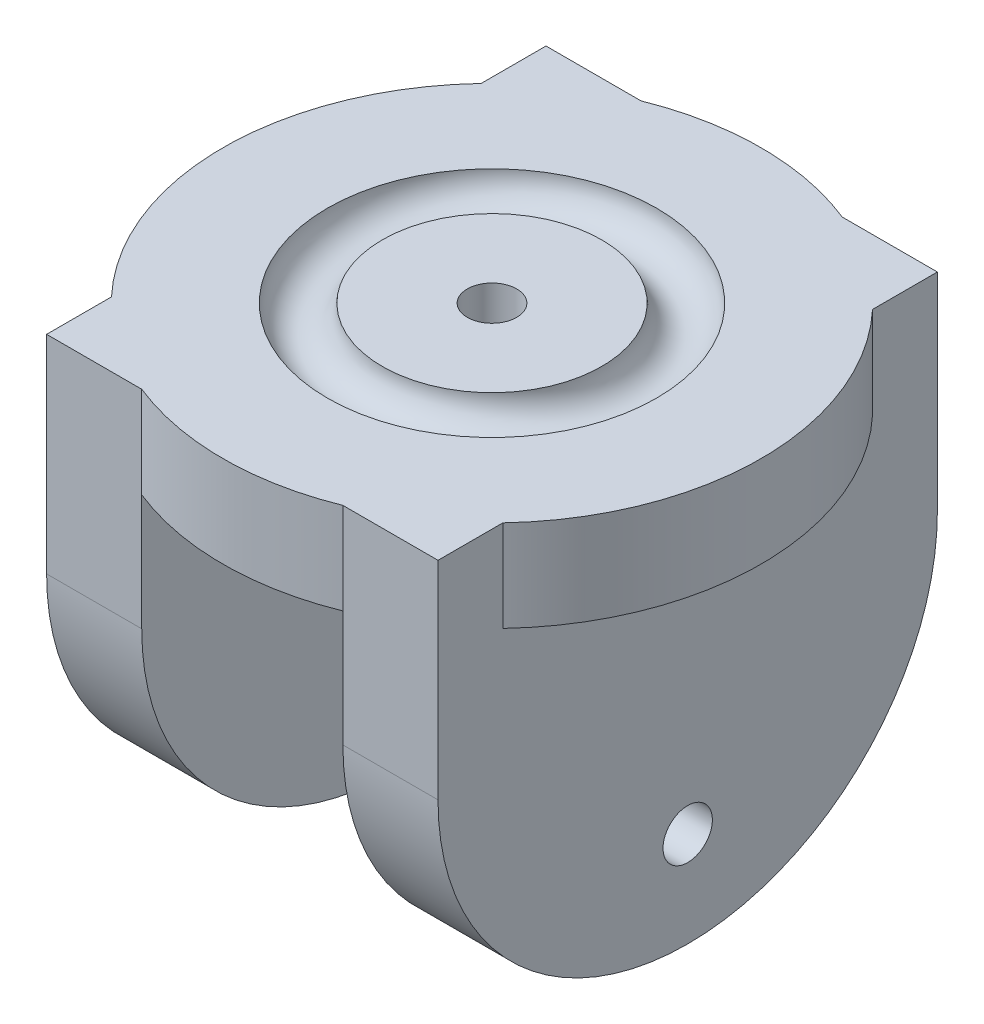
SolidWorks part; units mm, degrees
ref_plane "Front Plane" through (0, 0, 0) normal (0, 0, 1) x (1, 0, 0)
ref_plane "Top Plane" through (0, 0, 0) normal (0, 1, 0) x (1, 0, 0)
ref_plane "Right Plane" through (0, 0, 0) normal (1, 0, 0) x (0, 0, -1)
sketch "Sketch1" plane through (0, 0, 0) normal (0, 1, 0) x (1, 0, 0)
  circle A0 centre (0, 0) radius 29.441
extrude "Boss-Extrude1" add sketch "Sketch1" along normal blind 10 contours A0
sketch "Sketch2" plane through (0, 0, 0) normal (0, -1, 0) x (1, 0, 0)
  line L0 (-29.441, 0) -> (29.441, 0) construction
  line L1 (-21.4034, 27.3088) -> (-21.4034, -27.3088)
  line L2 (-21.4034, -27.3088) -> (-11, -27.3088)
  line L3 (-11, -27.3088) -> (-11, 27.3088)
  line L4 (-11, 27.3088) -> (-21.4034, 27.3088)
  line L5 (21.4034, 27.3088) -> (21.4034, -27.3088)
  line L6 (21.4034, -27.3088) -> (11, -27.3088)
  line L7 (11, -27.3088) -> (11, 27.3088)
  line L8 (11, 27.3088) -> (21.4034, 27.3088)
  line L9 (21.4034, -11.1622) -> (-21.4034, -11.1622) construction
  line L10 (0, 0) -> (0, -29.441) construction
  circle A0 centre (0, 0) radius 29.441 construction
  point P7 (0, 0)
  point P11 (-29.441, 0)
  point P16 (29.441, 0)
  point P22 (0, -11.1622)
  point P23 (0, 0)
  point P24 (-7.988, -28.3366)
  point P25 (12.4198, 25.0805)
  point P26 (12.344, 26.7282)
  dimension "D1" = 22
extrude "Boss-Extrude2" add sketch "Sketch2" along normal blind 40 and the other way up to surface (10 mm away) other way up to face at (0, 10, 29.441)
sketch "Sketch3" plane through (21.4034, 0, 0) normal (1, 0, 0) x (0, 0, -1)
  line L0 (0, -40) -> (0, 0) construction
  line L1 (27.3088, -40) -> (-27.3088, -40) construction
  circle A0 centre (0, -29.5844) radius 2.7
  point P4 (0, 0)
  point P8 (0, -34.3386)
  point P9 (0, -29.5844)
  dimension "D1" = 5.4
extrude "Cut-Extrude1" cut sketch "Sketch3" against normal blind 80
sketch "Sketch4" plane through (0, 10, 0) normal (0, 1, 0) x (1, 0, 0)
  circle A0 centre (0, 0) radius 2.7
  dimension "D1" = 5.4
extrude "Cut-Extrude2" cut sketch "Sketch4" along normal blind 80 and the other way blind 80
sketch "Sketch5" plane through (0, 10, 0) normal (0, 1, 0) x (1, 0, 0)
  circle A0 centre (0, 0) radius 15
  dimension "D1" = 30
sketch "Sketch6" plane through (0, 0, 0) normal (0, 0, 1) x (1, 0, 0)
  line L1 (15, 10) -> (-15, 10) construction
  circle A0 centre (-15, 10) radius 3
  point P2 (0, 0)
  dimension "D1" = 6
sweep "Cut-Sweep1" cut profiles "Sketch6" path "Sketch5"
sketch "Sketch8" plane through (-21.4034, 0, 0) normal (-1, 0, 0) x (0, 0, 1)
  line L0 (-27.3088, 10) -> (-27.3088, -40) construction
  line L1 (27.3088, 10) -> (27.3088, -40) construction
  line L2 (27.3088, -40) -> (-27.3088, -40) construction
  line L3 (-27.3088, -12.6912) -> (-33.5602, -12.6912)
  line L4 (-33.5602, -12.6912) -> (-33.5602, -51.8597)
  line L5 (-33.5602, -51.8597) -> (31.5458, -51.8597)
  line L6 (31.5458, -51.8597) -> (31.5458, -12.6912)
  line L7 (31.5458, -12.6912) -> (27.3088, -12.6912)
  line L8 (-27.3088, -12.6912) -> (27.3088, -12.6912) construction
  arc A0 (-27.3088, -12.6912) -> (27.3088, -12.6912) centre (0, -12.6912) ccw
  point P9 (26.7282, -18.6145)
extrude "Cut-Extrude3" cut sketch "Sketch8" against normal blind 80
